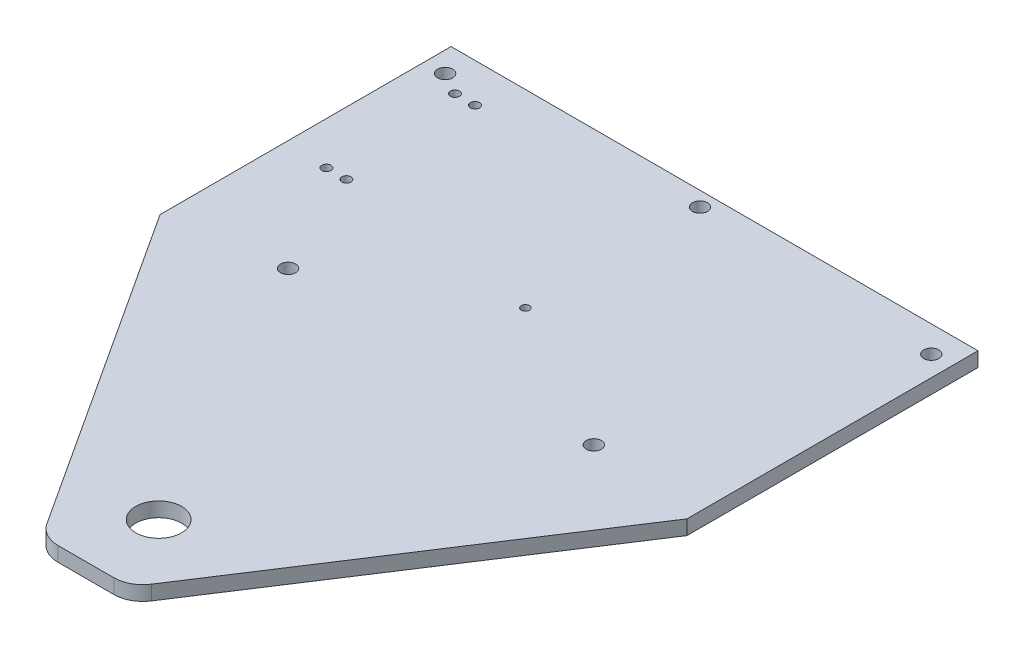
SolidWorks part; units mm, degrees
ref_plane "Front Plane" through (0, 0, 0) normal (0, 0, 1) x (1, 0, 0)
ref_plane "Top Plane" through (0, 0, 0) normal (0, 1, 0) x (1, 0, 0)
ref_plane "Right Plane" through (0, 0, 0) normal (1, 0, 0) x (0, 0, -1)
sketch "Sketch1" plane through (0, 16.315, 0) normal (0, 1, 0) x (1, 0, 0)
  line L0 (32.08, -22.225) -> (-15.875, -95.875)
  line L1 (-82.88, 41.275) -> (32.08, 41.275)
  line L2 (-82.88, 41.275) -> (-82.88, -22.225)
  line L3 (-82.88, -22.225) -> (32.08, -22.225)
  line L4 (32.08, 41.275) -> (32.08, -22.225)
  line L5 (-15.875, -95.875) -> (-34.925, -95.875)
  line L6 (-34.925, -95.875) -> (-82.88, -22.225)
  line L7 (-34.925, -95.875) -> (-15.875, -95.875) construction
  line L8 (-25.4, -95.875) -> (-25.4, -80) construction
  point P10 (-25.4, -80)
  point P12 (0, 0)
  point P16 (0, 0)
extrude "Boss-Extrude1" add sketch "Sketch1" along normal blind 3.175
sketch "Sketch2" plane through (0, 19.49, 0) normal (0, 1, 0) x (1, 0, 0)
  circle A0 centre (-25.4, 0) radius 0.889
  circle A1 centre (-25.4, 0) radius 11.95 construction
  circle A2 centre (-25.4, 0) radius 11.95 construction
  dimension "D1" = 1.778
extrude "Cut-Extrude1" cut sketch "Sketch2" against normal through all
sketch "Sketch3" plane through (0, 19.49, 0) normal (0, 1, 0) x (1, 0, 0)
  circle A0 centre (-25.4, -80) radius 5 construction
  circle A1 centre (-25.4, -80) radius 5
extrude "Cut-Extrude3" cut sketch "Sketch3" against normal through all
sketch "Sketch4" plane through (0, 19.49, 0) normal (0, 1, 0) x (1, 0, 0)
  circle A0 centre (-58.75, -18.415) radius 1.65 construction
  circle A1 centre (7.95, -18.415) radius 1.65 construction
  circle A2 centre (-25.4, 38.1) radius 1.65 construction
  circle A3 centre (27.635, 35.5324) radius 1.65 construction
  circle A4 centre (-78.435, 35.5324) radius 1.65 construction
  circle A5 centre (-58.75, -18.415) radius 1.65
  circle A6 centre (7.95, -18.415) radius 1.65
  circle A7 centre (-25.4, 38.1) radius 1.65
  circle A8 centre (27.635, 35.5324) radius 1.65
  circle A9 centre (-78.435, 35.5324) radius 1.65
  circle A10 centre (-73.5581, 4.75) radius 1 construction
  circle A11 centre (-69.1871, 4.75) radius 1 construction
  circle A12 centre (-69.1871, 32.8) radius 1 construction
  circle A13 centre (-73.5581, 32.8) radius 1 construction
  circle A14 centre (-73.5581, 4.75) radius 1
  circle A15 centre (-69.1871, 4.75) radius 1
  circle A16 centre (-69.1871, 32.8) radius 1
  circle A17 centre (-73.5581, 32.8) radius 1
extrude "Cut-Extrude5" cut sketch "Sketch4" against normal through all both and the other way through all
fillet "Fillet1" radius 6.35 2 edges at (-34.925, 17.9025, 95.875) (-15.875, 17.9025, 95.875)
